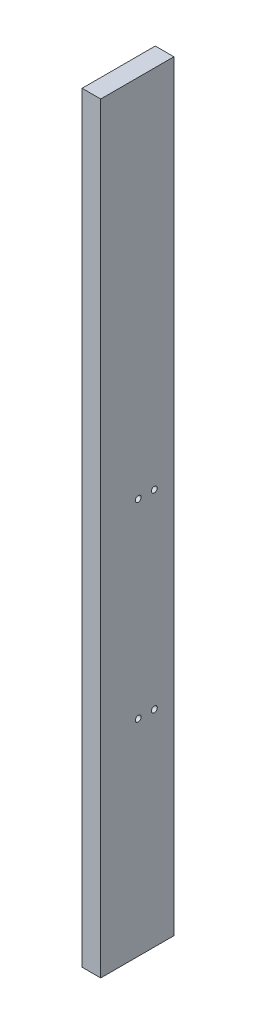
SolidWorks part; units mm, degrees
ref_plane "Front Plane" through (0, 0, 0) normal (0, 0, 1) x (1, 0, 0)
ref_plane "Top Plane" through (0, 0, 0) normal (0, 1, 0) x (1, 0, 0)
ref_plane "Right Plane" through (0, 0, 0) normal (1, 0, 0) x (0, 0, -1)
sketch "Sketch1" plane through (0, 0, 0) normal (1, 0, 0) x (0, 0, -1)
  line L1 (-25, 260) -> (25, 260)
  line L2 (-25, 260) -> (-25, -260)
  line L3 (-25, -260) -> (25, -260)
  line L4 (25, 260) -> (25, -260)
  line L5 (-25, 260) -> (25, -260) construction
  line L6 (-25, -260) -> (25, 260) construction
  point P0 (0, 0)
  dimension "D1" = 50
  dimension "D2" = 520
extrude "Boss-Extrude1" add sketch "Sketch1" along normal blind 12.7
sketch "Sketch5" plane through (0, 0, 0) normal (-1, 0, 0) x (0, 0, 1)
  circle A0 centre (-11.65, 10.6091) radius 2 construction
  circle A1 centre (-0.65, 10.6091) radius 2 construction
  circle A2 centre (-11.65, -119.3909) radius 2 construction
  circle A3 centre (-0.65, -119.3909) radius 2 construction
  circle A4 centre (-11.65, 10.6091) radius 2
  circle A5 centre (-0.65, 10.6091) radius 2
  circle A6 centre (-11.65, -119.3909) radius 2
  circle A7 centre (-0.65, -119.3909) radius 2
extrude "Cut-Extrude1" cut sketch "Sketch5" against normal through all
equation "\"width\"= 50mm"
equation "\"Length\"= 550mm"
